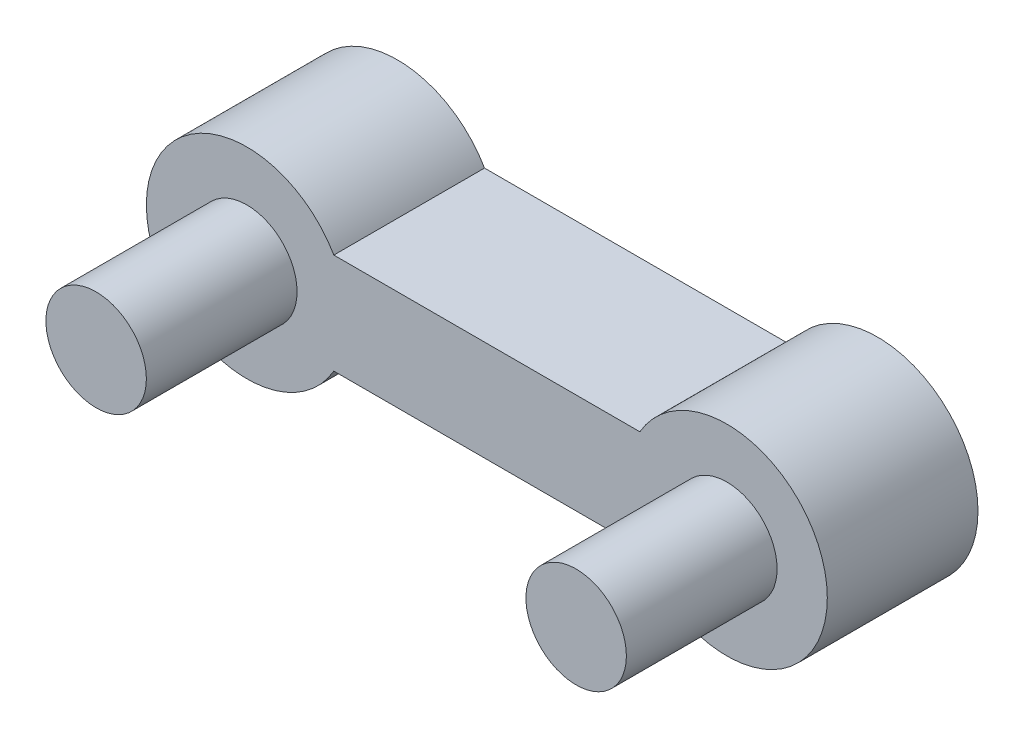
SolidWorks part; units mm, degrees
ref_plane "Спереди" through (0, 0, 0) normal (0, 0, 1) x (1, 0, 0)
ref_plane "Сверху" through (0, 0, 0) normal (0, 1, 0) x (1, 0, 0)
ref_plane "Справа" through (0, 0, 0) normal (1, 0, 0) x (0, 0, -1)
other "Configuration Table"
sketch "Sketch2" plane through (0, 0, 0) normal (0, 0, 1) x (1, 0, 0)
  line L1 (-36.505, 13.8003) -> (-30.4127, 13.8003)
  line L5 (-36.505, 11.8003) -> (-30.4127, 11.8003)
  line L7 (-13.5959, 12.8003) -> (-45.3291, 12.8003) construction
  arc A0 (-36.505, 13.8003) -> (-36.505, 11.8003) centre (-38.2371, 12.8003) ccw
  arc A2 (-30.4127, 13.8003) -> (-30.4127, 11.8003) centre (-28.6806, 12.8003) cw
  dimension "D3" = 4
  dimension "D1" = 2
  dimension "D2" = 9.5564
extrude "Boss-Extrude1" add sketch "Sketch2" along normal blind 3
ref_plane "Plane1" through (0, 0, 3) normal (0, 0, 1) x (1, 0, 0)
sketch "Sketch3" plane through (0, 0, 3) normal (0, 0, 1) x (1, 0, 0)
  circle A0 centre (-38.2371, 12.8003) radius 1
  circle A1 centre (-28.6806, 12.8003) radius 1
  dimension "D1" = 2
extrude "Boss-Extrude2" add sketch "Sketch3" along normal blind 3 contours A1 | A0
equation "\"R small\"= 2"
equation "\"R big\"= 4"
equation "\"width\"= 0.6"
equation "\"border width\"= 1"
equation "\"D3@Sketch2\"=\"R big\""
equation "\"D1@Sketch2\"=\"R small\""
equation "\"D1@Sketch3\"=\"R small\""
